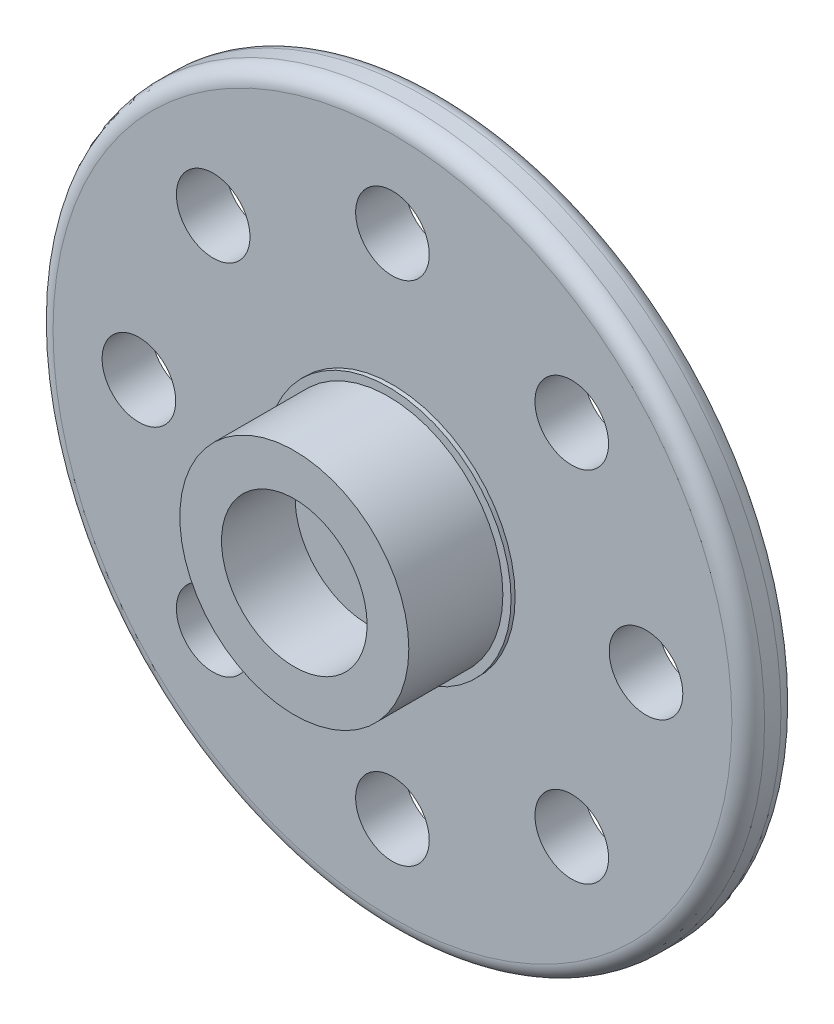
SolidWorks part; units mm, degrees
material "ABS"
ref_plane "Front Plane" through (0, 0, 0) normal (0, 0, 1) x (1, 0, 0)
ref_plane "Top Plane" through (0, 0, 0) normal (0, 1, 0) x (1, 0, 0)
ref_plane "Right Plane" through (0, 0, 0) normal (1, 0, 0) x (0, 0, -1)
sketch "Sketch1" plane through (0, 0, 0) normal (0, 0, 1) x (1, 0, 0)
  circle A0 centre (0, 0) radius 217.5
extrude "Boss-Extrude1" add sketch "Sketch1" along normal blind 30 contours A0
sketch "Sketch2" plane through (0, 0, 30) normal (0, 0, 1) x (1, 0, 0)
  circle A0 centre (0, 0) radius 75
extrude "Boss-Extrude2" add sketch "Sketch2" along normal blind 2.5 contours A0
sketch "Sketch3" plane through (0, 0, 32.5) normal (0, 0, 1) x (1, 0, 0)
  circle A0 centre (0, 0) radius 70
extrude "Boss-Extrude3" add sketch "Sketch3" along normal blind 57.5
sketch "Sketch12" plane through (0, 0, 30) normal (0, 0, 1) x (1, 0, 0)
  line L0 (155, 0) -> (109.6016, 109.6016) construction
  line L1 (109.6016, 109.6016) -> (0, 155) construction
  line L2 (0, 155) -> (-109.6016, 109.6016) construction
  line L3 (-109.6016, 109.6016) -> (-155, 0) construction
  line L4 (-155, 0) -> (-109.6016, -109.6016) construction
  line L5 (-109.6016, -109.6016) -> (0, -155) construction
  line L6 (0, -155) -> (109.6016, -109.6016) construction
  line L7 (109.6016, -109.6016) -> (155, 0) construction
  line L8 (155, 0) -> (-155, 0) construction
  line L9 (0, 155) -> (0, -155) construction
  circle A0 centre (0, 155) radius 22.5
  circle A1 centre (109.6016, 109.6016) radius 22.5
  circle A2 centre (155, 0) radius 22.5
  circle A3 centre (109.6016, -109.6016) radius 22.5
  circle A4 centre (0, -155) radius 22.5
  circle A5 centre (-109.6016, -109.6016) radius 22.5
  circle A6 centre (-155, 0) radius 22.5
  circle A7 centre (-109.6016, 109.6016) radius 22.5
  point P2 (0, 0)
  dimension "D1" = 310
  dimension "D3" = 45
  dimension "D2" = 135
extrude "Cut-Extrude2" cut sketch "Sketch12" against normal up to surface (30 mm away) up to face at (217.5, 0, 0)
fillet "Fillet2" radius 10 2 edges at (217.5, 0, 0) (217.5, 0, 30)
scale "Scale2" scale about centroid uniform scaling yes scale factor 0.1
sketch "Sketch14" plane through (0, 0, 30.0767) normal (0, 0, 1) x (1, 0, 0)
  circle A0 centre (0, 0) radius 4.45
  dimension "D1" = 8.9
extrude "Cut-Extrude3" cut sketch "Sketch14" against normal blind 4.5
